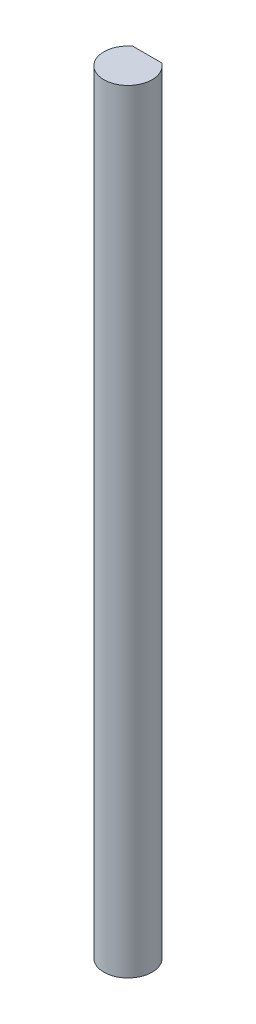
SolidWorks part; units mm, degrees
ref_plane "Front Plane" through (0, 0, 0) normal (0, 0, 1) x (1, 0, 0)
ref_plane "Top Plane" through (0, 0, 0) normal (0, 1, 0) x (1, 0, 0)
ref_plane "Right Plane" through (0, 0, 0) normal (1, 0, 0) x (0, 0, -1)
sketch "Sketch1" plane through (0, 0, 0) normal (0, 1, 0) x (1, 0, 0)
  line L0 (-1.905, 2.54) -> (1.905, 2.54)
  arc A0 (-1.905, 2.54) -> (1.905, 2.54) centre (0, 0) ccw
  dimension "D1" = 6.35
  dimension "D2" = 2.54
extrude "Boss-Extrude1" add sketch "Sketch1" along normal blind 101.6
